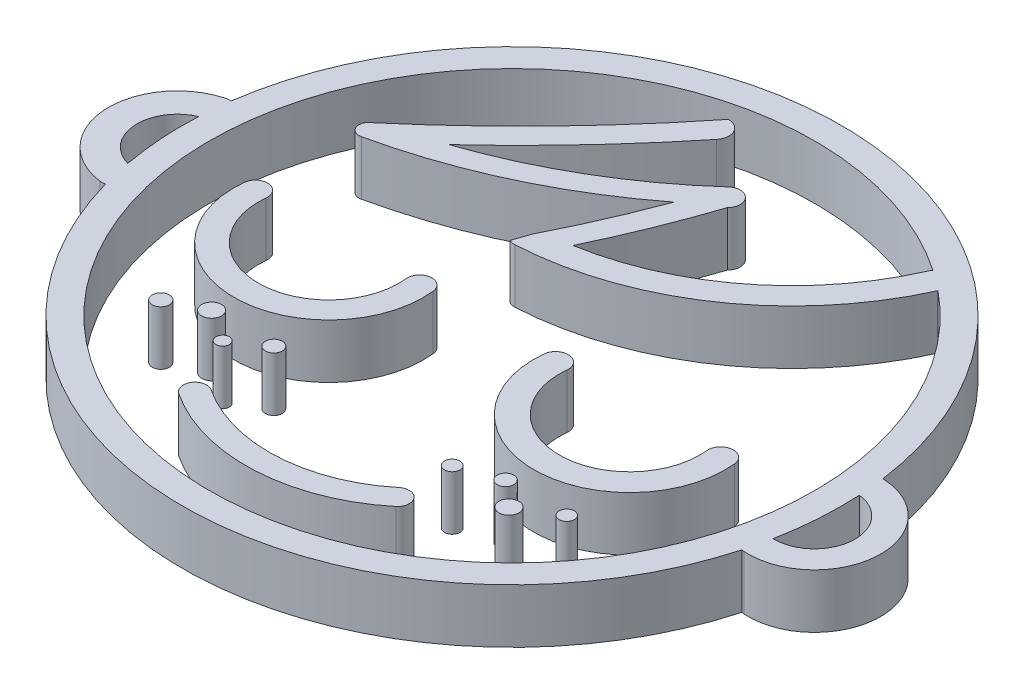
SolidWorks part; units mm, degrees
ref_plane "Alzado" through (0, 0, 0) normal (0, 0, 1) x (1, 0, 0)
ref_plane "Planta" through (0, 0, 0) normal (0, 1, 0) x (1, 0, 0)
ref_plane "Vista lateral" through (0, 0, 0) normal (1, 0, 0) x (0, 0, -1)
sketch "Croquis1" plane through (0, 0, 0) normal (0, 1, 0) x (1, 0, 0)
  line L0 (0, 0) -> (0, 60) construction
  line L1 (45.4256, 39.2063) -> (44.9931, 37.9533)
  line L2 (4.4846, 33.2062) -> (87.8694, 33.2062) construction
  line L3 (50.2659, -3.2973) -> (49.6429, 66.0717) construction
  arc A0 (62.518, 51.6572) -> (64.0132, 50.5391) centre (49.8858, 33.2062) ccw
  arc A1 (74.0069, 36.4621) -> (25.7787, 36.5645) centre (49.8858, 33.2062) ccw
  arc A2 (47.6409, 39.9502) -> (62.4243, 51.4925) centre (44.2991, 59.4687) ccw
  arc A3 (31.4718, 31.8621) -> (45.4048, 31.8621) centre (38.4383, 31.1201) ccw
  arc A4 (33.2714, 31.6704) -> (43.6051, 31.6704) centre (38.4383, 31.1201) ccw
  arc A5 (33.2714, 31.6704) -> (31.4718, 31.8621) centre (32.3716, 31.7663) ccw
  arc A6 (45.4048, 31.8621) -> (43.6051, 31.6704) centre (44.5049, 31.7663) ccw
  arc A7 (47.6409, 39.9502) -> (50.9184, 48.0743) centre (-14.6018, 69.7838) ccw
  arc A8 (53.5136, 31.9586) -> (67.571, 31.9586) centre (60.5423, 31.2324) ccw
  arc A9 (55.3815, 31.7656) -> (65.7031, 31.7656) centre (60.5423, 31.2324) ccw
  arc A10 (55.3815, 31.7656) -> (53.5136, 31.9586) centre (54.4475, 31.8621) ccw
  arc A11 (67.571, 31.9586) -> (65.7031, 31.7656) centre (66.637, 31.8621) ccw
  circle A12 centre (35.8992, 21.2576) radius 0.6341
  circle A13 centre (38.4383, 22.4698) radius 0.7334
  circle A14 centre (40.7947, 20.9312) radius 0.4956
  circle A15 centre (43.0326, 22.4698) radius 0.6255
  circle A16 centre (57.2527, 21.4268) radius 0.573
  circle A17 centre (60.1434, 22.4698) radius 0.6136
  circle A18 centre (62.0083, 20.8538) radius 0.7387
  circle A19 centre (64.6659, 22.4698) radius 0.5595
  arc A21 (42.5564, 15.924) -> (57.8014, 16.7238) centre (49.6397, 26.6026) ccw
  arc A22 (43.5088, 17.3597) -> (56.7041, 18.0519) centre (49.6397, 26.6026) ccw
  arc A23 (43.5088, 17.3597) -> (42.5564, 15.924) centre (43.0326, 16.6419) ccw
  arc A24 (57.8014, 16.7238) -> (56.7041, 18.0519) centre (57.2527, 17.3879) ccw
  arc A26 (25.3733, 36.5331) -> (26.0467, 26.6012) centre (26.7365, 31.6367) ccw
  arc A27 (25.574, 34.3755) -> (25.9543, 28.7661) centre (26.7365, 31.6367) ccw
  arc A28 (25.7787, 36.5645) -> (25.3733, 36.5331) centre (25.6559, 35.518) ccw
  arc A29 (26.0467, 26.6012) -> (26.4526, 26.6248) centre (26.1897, 27.6451) ccw
  arc A31 (73.5176, 26.6969) -> (74.1799, 36.4662) centre (73.8488, 31.5816) ccw
  arc A32 (73.7834, 28.5871) -> (74.1882, 34.5574) centre (73.8488, 31.5816) ccw
  arc A33 (73.3467, 26.7243) -> (73.5176, 26.6969) centre (73.5819, 27.6451) ccw
  arc A34 (74.1799, 36.4662) -> (74.0069, 36.4621) centre (74.1157, 35.518) ccw
  arc A36 (45.4539, 37.8574) -> (64.0132, 50.5391) centre (44.2991, 59.4687) ccw
  arc A38 (44.9931, 37.9533) -> (45.4539, 37.8574) centre (45.4048, 38.7759) ccw
  arc A39 (62.518, 51.6572) -> (62.4243, 51.4925) centre (63.2662, 51.122) ccw
  arc A41 (36.6046, 41.8185) -> (49.6429, 49.4386) centre (24.4461, 77.5866) ccw
  arc A42 (32.2272, 40.2595) -> (45.3133, 53.752) centre (-28.8919, 112.6301) ccw
  arc A43 (32.2272, 40.2595) -> (33.0468, 39.1689) centre (32.7056, 39.7658) ccw
  arc A44 (46.1636, 52.0434) -> (45.3133, 53.752) centre (45.3557, 52.7072) ccw
  arc A46 (32.8788, 39.1004) -> (48.5977, 46.4579) centre (24.4461, 77.5866) ccw
  arc A47 (73.7834, 28.5871) -> (74.1882, 34.5574) centre (49.8858, 33.2062) ccw
  arc A48 (25.574, 34.3755) -> (25.9543, 28.7661) centre (49.8858, 33.2062) ccw
  arc A49 (50.8889, 48.0467) -> (49.6429, 49.4386) centre (50.2659, 48.7427) ccw
  arc A52 (45.4256, 39.2063) -> (48.5977, 46.4579) centre (-14.6018, 69.7838) ccw
  arc A54 (36.6046, 41.8185) -> (46.1636, 52.0434) centre (-28.8919, 112.6301) ccw
  arc A55 (26.4526, 26.6248) -> (73.3467, 26.7243) centre (49.8858, 33.2062) ccw
  point P9 (38.4383, 25.0191)
  point P14 (60.5423, 25.1052)
  point P41 (50.2659, 14.6662)
  point P46 (22.7168, 31.3642)
  point P54 (77.7852, 31.3147)
  point P65 (56.0819, 42.4223)
  point P70 (39.1778, 45.8874)
  point P78 (41.9148, 43.0398)
  point P86 (48.41, 43.7057)
  dimension "D2" = 44.7218
  dimension "D1" = 60
extrude "Saliente-Extruir1" add sketch "Croquis1" along normal blind 4
sketch "Croquis8" plane through (0, 0, 0) normal (0, -1, 0) x (1, 0, 0)
  line L2 (23.5858, -33.2062) -> (23.5858, -59.5062)
  line L3 (23.5858, -59.5062) -> (76.1858, -59.5062)
  line L4 (76.1858, -33.2062) -> (76.1858, -59.5062)
  arc A0 (76.1858, -33.2062) -> (23.5858, -33.2062) centre (49.8858, -33.2062) ccw
  dimension "D1" = 52.6
  dimension "D2" = 26.3
equation "\"ç\"=0.5"
